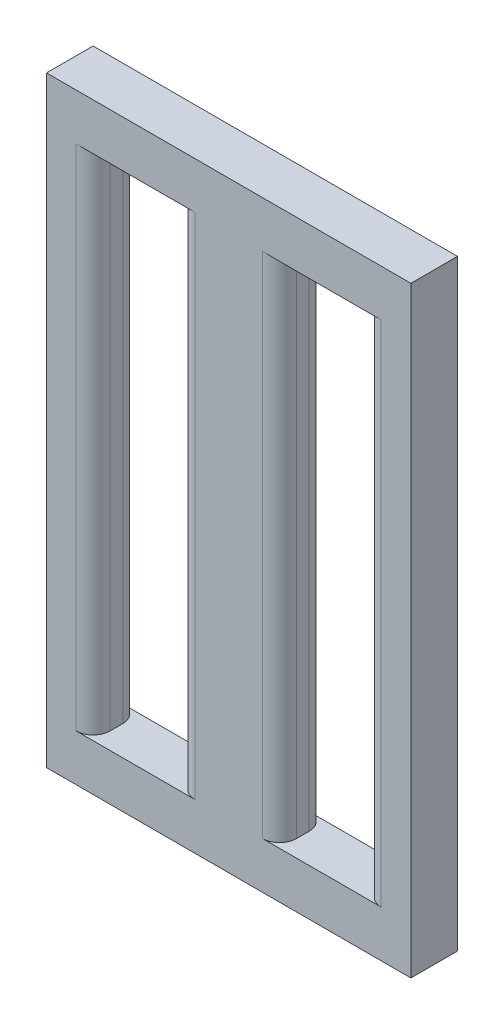
SolidWorks part; units mm, degrees
material "ABS"
ref_plane "Front Plane" through (0, 0, 0) normal (0, 0, 1) x (1, 0, 0)
ref_plane "Top Plane" through (0, 0, 0) normal (0, 1, 0) x (1, 0, 0)
ref_plane "Right Plane" through (0, 0, 0) normal (1, 0, 0) x (0, 0, -1)
sketch "Sketch1" plane through (0, 0, 0) normal (0, 0, 1) x (1, 0, 0)
  line L0 (0, 30) -> (0, 32.75)
  line L1 (0, 0) -> (2.75, 0) construction
  line L2 (0, 0) -> (0, 30)
  line L3 (0, 30) -> (2.75, 30) construction
  line L4 (2.75, 0) -> (2.75, 30)
  line L5 (7.75, 0) -> (13.75, 0) construction
  line L6 (7.75, 0) -> (7.75, 30)
  line L7 (7.75, 30) -> (13.75, 30) construction
  line L8 (13.75, 0) -> (13.75, 30)
  line L9 (21.5, 0) -> (18.75, 0) construction
  line L10 (21.5, 0) -> (21.5, 30)
  line L11 (21.5, 30) -> (18.75, 30) construction
  line L12 (18.75, 0) -> (18.75, 30)
  line L13 (2.75, 30) -> (7.75, 30)
  line L14 (13.75, 30) -> (18.75, 30)
  line L15 (2.75, 0) -> (7.75, 0)
  line L16 (13.75, 0) -> (18.75, 0)
  line L17 (0, 32.75) -> (21.5, 32.75)
  line L18 (21.5, 32.75) -> (21.5, 30)
  line L19 (0, 0) -> (0, -2.75)
  line L20 (0, -2.75) -> (21.5, -2.75)
  line L21 (21.5, -2.75) -> (21.5, 0)
  line L22 (0, 15) -> (2.75, 15) construction
  line L23 (18.75, 15) -> (21.5, 15) construction
  dimension "D1" = 30
  dimension "D2" = 2.75
  dimension "D3" = 5
  dimension "D4" = 2.75
  dimension "D5" = 21.5
extrude "Boss-Extrude1" add sketch "Sketch1" along normal blind 2.75
fillet "Fillet1" radius 1 8 edges at (2.75, 15, 2.75) (2.75, 15, 0) (18.75, 15, 2.75) (18.75, 15, 0) (7.75, 15, 0) (13.75, 15, 0) (13.75, 15, 2.75) (7.75, 15, 2.75)
